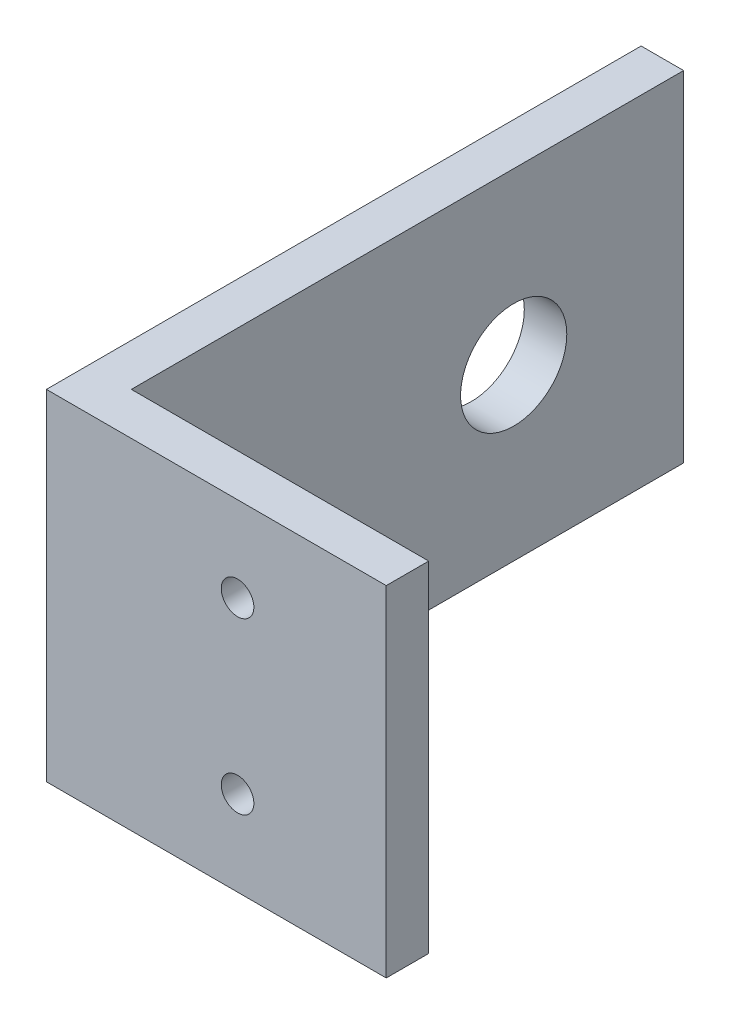
SolidWorks part; units mm, degrees
material "6061-T6 (SS)"
ref_plane "Front Plane" through (0, 0, 0) normal (0, 0, 1) x (1, 0, 0)
ref_plane "Top Plane" through (0, 0, 0) normal (0, 1, 0) x (1, 0, 0)
ref_plane "Right Plane" through (0, 0, 0) normal (1, 0, 0) x (0, 0, -1)
sketch "Sketch1" plane through (0, 0, 0) normal (0, 1, 0) x (1, 0, 0)
  line L0 (0, 0) -> (0, 44.45)
  line L1 (0, 0) -> (25.4, 0)
  line L4 (25.4, 0) -> (25.4, 3.175)
  line L5 (0, 44.45) -> (3.175, 44.45)
  line L6 (3.175, 44.45) -> (3.175, 3.175)
  line L7 (3.175, 3.175) -> (25.4, 3.175)
  dimension "D1" = 25.4
  dimension "D2" = 44.45
  dimension "D3" = 3.175
extrude "Boss-Extrude1" add sketch "Sketch1" along normal blind 25.4
sketch "Sketch2" plane through (3.175, 0, 0) normal (1, 0, 0) x (0, 0, -1)
  line L0 (44.45, 25.4) -> (44.45, 0) construction
  line L1 (3.175, 0) -> (44.45, 0) construction
  circle A0 centre (31.75, 12.7) radius 3.9687
  dimension "D1" = 7.9375
  dimension "D2" = 12.7
  dimension "D3" = 12.7
extrude "Cut-Extrude1" cut sketch "Sketch2" against normal through all
sketch "Sketch3" plane through (0, 0, -3.175) normal (0, 0, -1) x (-1, 0, 0)
  line L0 (-14.2875, 0) -> (-14.2875, 25.4) construction
  line L1 (-25.4, 0) -> (-3.175, 0) construction
  line L2 (-25.4, 25.4) -> (-3.175, 25.4) construction
  circle A0 centre (-14.2875, 19.05) radius 1.5875 construction
  circle A1 centre (-14.2875, 6.35) radius 1.5875 construction
  dimension "D1" = 6.35
  dimension "D2" = 12.7
  dimension "D3" = 3.175
hole_wizard "CSK for #2 Flat Head Machine Screw1" positions "Sketch4" profile "Sketch5" countersink size "#2" standard "ANSI Inch" end condition through all
sketch "Sketch4" plane through (0, 0, -3.175) normal (0, 0, -1) x (-1, 0, 0)
  point P0 (-14.2875, 19.05)
  point P3 (-14.2875, 6.35)
sketch "Sketch5" plane through (14.2875, 19.05, -3.175) normal (1, 0, 0) x (0, 1, 0)
  line L0 (0, 0) -> (0, 3.175)
  line L1 (0, 3.175) -> (1.2192, 3.175)
  line L2 (1.2192, 3.175) -> (1.2192, 1.1103)
  line L3 (1.2192, 1.1103) -> (2.1844, 0)
  line L5 (2.1844, 0) -> (0, 0)
  line L6 (-1.2192, 1.1103) -> (-2.1844, 0) construction
  line L11 (0, -6.35) -> (0, 107.95) construction
  dimension "Thru Hole Dia." = 2.4384
  dimension "Thru Hole Depth" = 3.175
  dimension "Near C'Sink Dia." = 4.3688
  dimension "Near C'Sink Angle" = 82
equation "\"Thick\"= \"in\""
